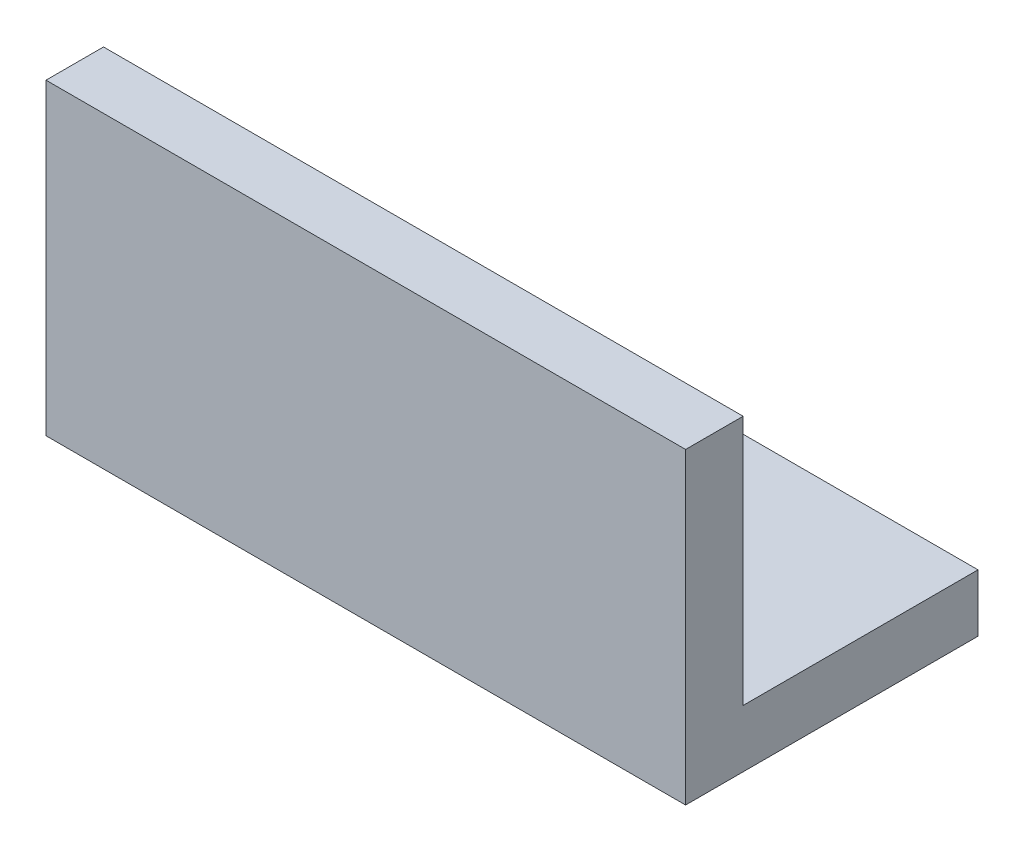
SolidWorks part; units mm, degrees
ref_plane "Front Plane" through (0, 0, 0) normal (0, 0, 1) x (1, 0, 0)
ref_plane "Top Plane" through (0, 0, 0) normal (0, 1, 0) x (1, 0, 0)
ref_plane "Right Plane" through (0, 0, 0) normal (1, 0, 0) x (0, 0, -1)
sketch "Sketch1" plane through (0, 0, 0) normal (0, 1, 0) x (1, 0, 0)
  line L1 (0, 0) -> (76.708, 0)
  line L5 (0, 0) -> (0, 32.28)
  line L6 (0, 32.28) -> (76.708, 32.28)
  line L8 (76.708, 32.28) -> (76.708, 0)
  line L9 (0, 0) -> (38.354, 32.28) construction
  line L10 (76.708, 0) -> (38.354, 32.28) construction
  line L11 (19.177, 16.14) -> (57.531, 16.14) construction
  circle A0 centre (19.177, 16.14) radius 3.5719
  circle A1 centre (19.177, 16.14) radius 7.9375 construction
  circle A2 centre (57.531, 16.14) radius 3.5719
  circle A3 centre (57.531, 16.14) radius 7.9375 construction
  point P1 (0, 0)
  point P10 (38.354, 32.28)
  point P14 (0, 0.3498)
  point P15 (38.354, 32.28)
  point P16 (61.0089, 0)
  point P17 (0, 0)
  point P18 (29.828, 15.5439)
  point P19 (0, 0)
  point P20 (59.6427, 0)
  point P21 (57.531, 16.14)
  point P22 (76.708, 0)
  point P23 (38.354, 32.28)
  point P24 (0, 0)
  dimension "D3" = 7.1437
  dimension "D4" = 15.875
  dimension "D5" = 7.1437
  dimension "D6" = 15.875
  dimension "D1" = 38.354
  dimension "D2" = 32.28
extrude "Main Body" add sketch "Sketch1" along normal blind 34
sketch "Sketch3" plane through (0, 0, 0) normal (0, 0, 1) x (1, 0, 0)
  line L0 (0, 0) -> (38.354, 21.1841) construction
  line L2 (76.708, 0) -> (38.354, 21.1841) construction
  line L3 (0, 34) -> (76.708, 34) construction
  line L4 (19.177, 10.592) -> (57.531, 10.592) construction
  circle A0 centre (19.177, 10.592) radius 3.5719
  circle A1 centre (19.177, 10.592) radius 7.9375 construction
  circle A2 centre (57.531, 10.592) radius 3.5719
  circle A3 centre (57.531, 10.592) radius 7.9375 construction
  point P7 (32.28, 21.1841)
  point P19 (38.354, 34)
  dimension "D1" = 7.1437
  dimension "D2" = 15.875
  dimension "D3" = 7.1437
  dimension "D4" = 15.875
extrude "9/32 Right Rail" [suppressed] cut sketch "Sketch3" against normal blind 8.3344 and the other way through all
sketch "Sketch13" plane through (0, 34, 0) normal (0, 1, 0) x (1, 0, 0)
  line L1 (0, 32.28) -> (0, 0) construction
  line L5 (76.708, 32.28) -> (0, 32.28)
  line L6 (76.708, 32.28) -> (76.708, 6.35)
  line L11 (76.708, 6.35) -> (0, 6.35)
  line L13 (0, 32.28) -> (0, 6.35)
  line L14 (0, 0) -> (76.708, 0) construction
  dimension "D1" = 6.35
extrude "Cut-Extrude1" cut sketch "Sketch13" against normal offset from surface (27.65 mm away) 6.35 up to face at (19.177, 0, -12.5681)
sketch "Sketch14" plane through (0, 0, 0) normal (0, -1, 0) x (1, 0, 0)
  line L0 (0, 0) -> (76.708, 0) construction
  line L1 (73.66, 0) -> (3.048, 0)
  line L2 (73.66, 0) -> (73.66, -32.28)
  line L3 (73.66, -32.28) -> (3.048, -32.28)
  line L4 (3.048, 0) -> (3.048, -32.28)
  line L5 (76.708, -32.28) -> (0, -32.28) construction
  line L6 (0, -32.28) -> (0, 0) construction
  line L7 (76.708, 0) -> (76.708, -32.28) construction
  point P8 (50.369, 0)
  dimension "D1" = 3.048
  dimension "D2" = 3.048
extrude "Cut-Extrude2" cut sketch "Sketch14" against normal through all both and the other way through all flip side to cut
